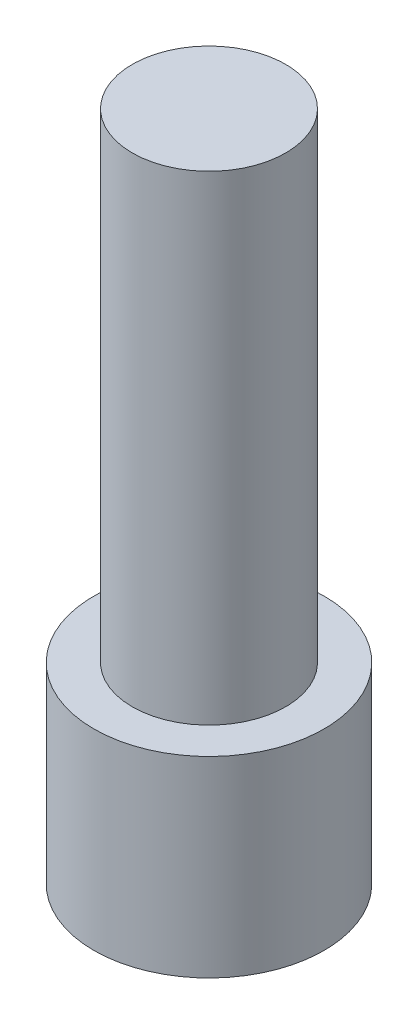
SolidWorks part; units mm, degrees
ref_plane "Front Plane" through (0, 0, 0) normal (0, 0, 1) x (1, 0, 0)
ref_plane "Top Plane" through (0, 0, 0) normal (0, 1, 0) x (1, 0, 0)
ref_plane "Right Plane" through (0, 0, 0) normal (1, 0, 0) x (0, 0, -1)
sketch "Sketch1" plane through (0, 0, 0) normal (0, 1, 0) x (1, 0, 0)
  circle A0 centre (0, 0) radius 4
  dimension "D1" = 8
extrude "Boss-Extrude1" add sketch "Sketch1" along normal blind 25
sketch "Sketch2" plane through (0, 0, 0) normal (0, -1, 0) x (1, 0, 0)
  circle A0 centre (0, 0) radius 6
  circle A1 centre (0, 0) radius 4
  circle A2 centre (0, 0) radius 4
  circle M3 centre (0, 0) radius 4
  dimension "D1" = 0
  dimension "D2" = 2
extrude "Boss-Extrude2" add sketch "Sketch2" along normal blind 3 contours A0 M3 | M3 | A2
sketch "Sketch3" plane through (0, -3, 0) normal (0, -1, 0) x (1, 0, 0)
  line L1 (4.6188, 0) -> (2.3094, 4)
  line L2 (2.3094, 4) -> (-2.3094, 4)
  line L3 (-2.3094, 4) -> (-4.6188, 0)
  line L4 (-4.6188, 0) -> (-2.3094, -4)
  line L5 (-2.3094, -4) -> (2.3094, -4)
  line L6 (2.3094, -4) -> (4.6188, 0)
  circle A0 centre (0, 0) radius 4 construction
  circle A1 centre (0, 0) radius 6
  circle A2 centre (0, 0) radius 6
  point P0 (0, 0)
  dimension "D2" = 8
  dimension "D1" = 0
extrude "Boss-Extrude3" add sketch "Sketch3" along normal blind 7
